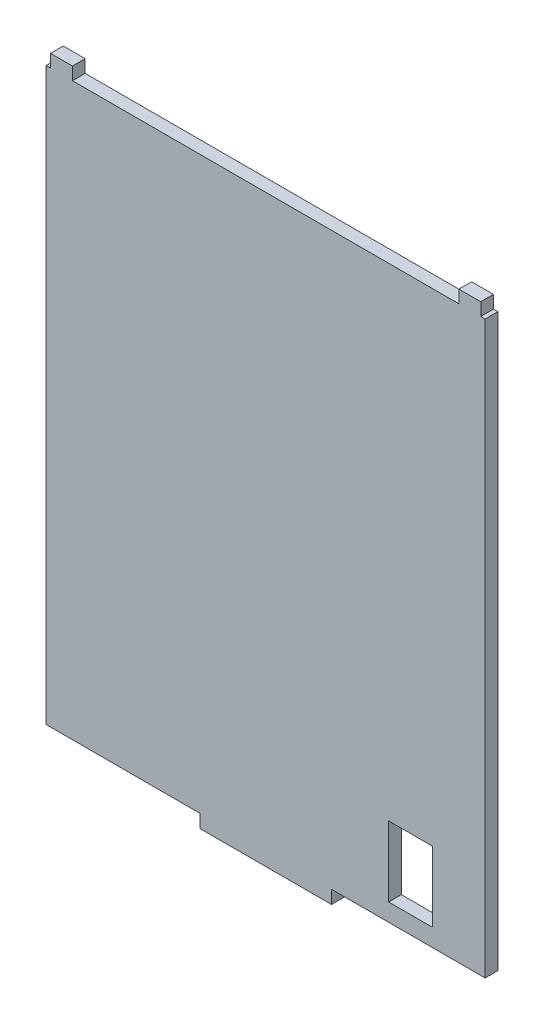
SolidWorks part; units mm, degrees
ref_plane "前视基准面" through (0, 0, 0) normal (0, 0, 1) x (1, 0, 0)
ref_plane "上视基准面" through (0, 0, 0) normal (0, 1, 0) x (1, 0, 0)
ref_plane "右视基准面" through (0, 0, 0) normal (1, 0, 0) x (0, 0, -1)
sketch "草图1" plane through (0, 0, 0) normal (0, 0, 1) x (1, 0, 0)
  line L0 (65, 0) -> (100, 0)
  line L1 (0, 0) -> (35, 0)
  line L2 (0, 0) -> (0, 130)
  line L3 (6, 130) -> (94, 130)
  line L4 (100, 0) -> (100, 130)
  line L7 (50, -3) -> (65, -3)
  line L8 (65, 0) -> (65, -3)
  line L11 (50, -3) -> (35, -3)
  line L12 (35, 0) -> (35, -3)
  line L13 (50, -3) -> (50, 0)
  line L16 (1, 132.9) -> (5, 132.9)
  line L20 (99, 132.9) -> (95, 132.9)
  line L22 (50, 0) -> (50, 4)
  line L23 (50, 4) -> (94, 4)
  line L24 (94, 4) -> (88, 4)
  line L25 (88, 4) -> (88, 20)
  line L26 (88, 20) -> (83, 20)
  line L29 (5, 132.9) -> (6, 132.9)
  line L32 (6, 132.9) -> (6, 130)
  line L33 (0, 130) -> (1, 130)
  line L36 (1, 130) -> (1, 132.9)
  line L37 (95, 132.9) -> (94, 132.9)
  line L40 (94, 132.9) -> (94, 130)
  line L41 (100, 130) -> (99, 130)
  line L44 (99, 130) -> (99, 132.9)
  line L45 (83, 4) -> (78, 4)
  line L47 (83, 20) -> (78, 20)
  line L48 (78, 4) -> (78, 20)
extrude "凸台-拉伸1" add sketch "草图1" along normal blind 2.9
